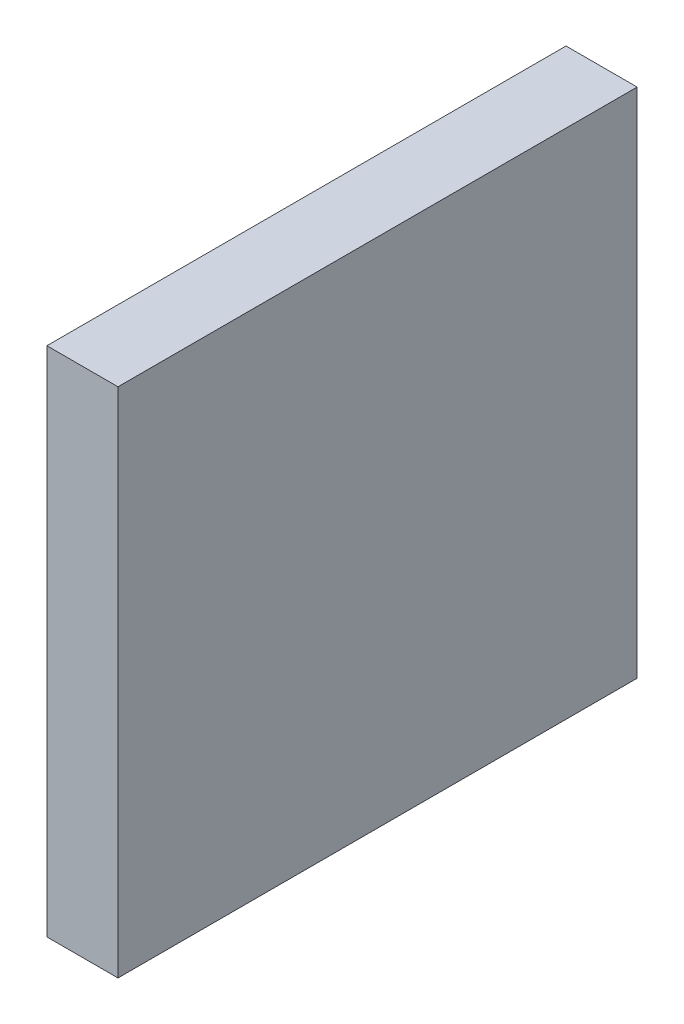
SolidWorks part; units mm, degrees
ref_plane "Front Plane" through (0, 0, 0) normal (0, 0, 1) x (1, 0, 0)
ref_plane "Top Plane" through (0, 0, 0) normal (0, 1, 0) x (1, 0, 0)
ref_plane "Right Plane" through (0, 0, 0) normal (1, 0, 0) x (0, 0, -1)
sketch "Sketch2" plane through (0, 0, 0) normal (1, 0, 0) x (0, 0, -1)
  line L1 (0, 0) -> (46.355, 0)
  line L2 (0, 0) -> (0, 45.72)
  line L3 (0, 45.72) -> (46.355, 45.72)
  line L4 (46.355, 0) -> (46.355, 45.72)
  dimension "D1" = 45.72
  dimension "D2" = 46.355
extrude "Boss-Extrude1" add sketch "Sketch2" along normal blind 6.35
